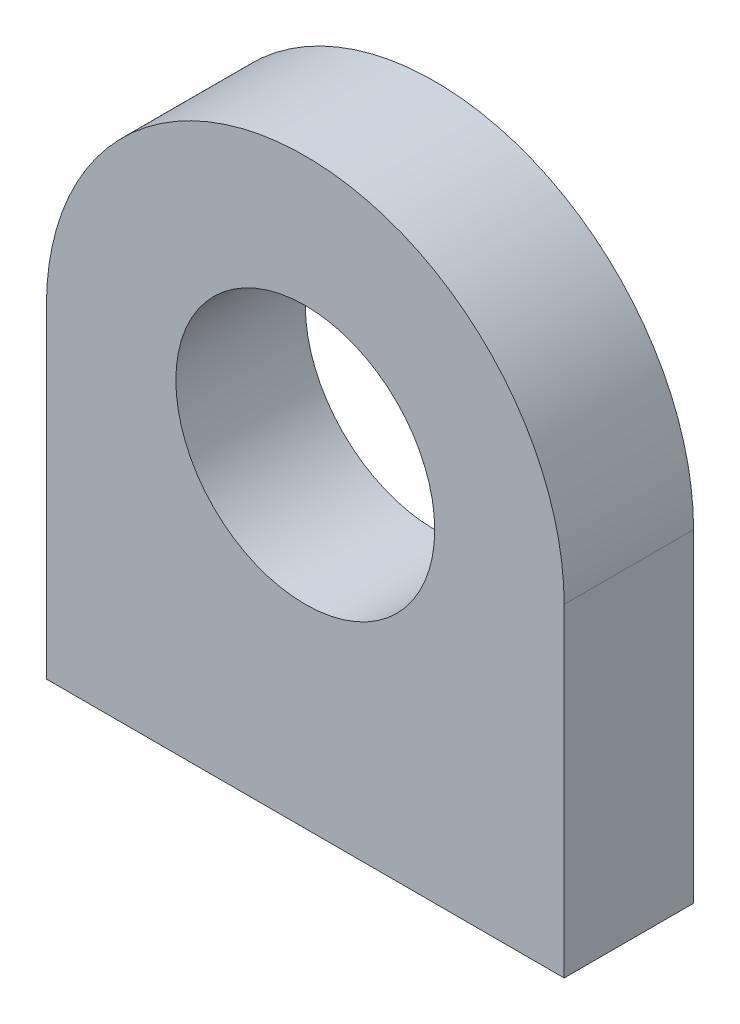
SolidWorks part; units mm, degrees
ref_plane "Alzado" through (0, 0, 0) normal (0, 0, 1) x (1, 0, 0)
ref_plane "Planta" through (0, 0, 0) normal (0, 1, 0) x (1, 0, 0)
ref_plane "Vista lateral" through (0, 0, 0) normal (1, 0, 0) x (0, 0, -1)
sketch "Croquis1" plane through (0, 0, 0) normal (0, 0, 1) x (1, 0, 0)
  line L0 (-8, 0) -> (-8, -10)
  line L1 (-8, -10) -> (8, -10)
  line L2 (8, -10) -> (8, 0)
  circle A0 centre (0, 0) radius 4
  arc A1 (8, 0) -> (-8, 0) centre (0, 0) ccw
  dimension "D1" = 8
  dimension "D2" = 4
  dimension "D3" = 10
extrude "Saliente-Extruir1" add sketch "Croquis1" along normal blind 4
